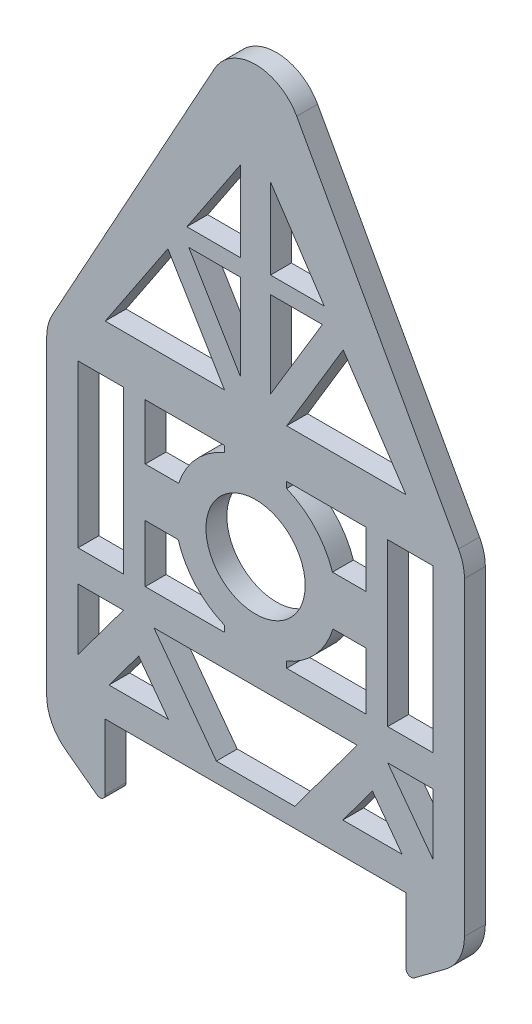
SolidWorks part; units mm, degrees
ref_plane "Front Plane" through (0, 0, 0) normal (0, 0, 1) x (1, 0, 0)
ref_plane "Top Plane" through (0, 0, 0) normal (0, 1, 0) x (1, 0, 0)
ref_plane "Right Plane" through (0, 0, 0) normal (1, 0, 0) x (0, 0, -1)
sketch "Sketch1" plane through (0, 0, 0) normal (0, 0, 1) x (1, 0, 0)
  line L0 (-99.8035, -268.9774) -> (188.0854, -268.9774)
  line L1 (244.1409, -268.9774) -> (244.1409, 31.0226)
  line L2 (-155.8591, 31.0226) -> (-155.8591, -268.9774)
  line L3 (-155.8591, -268.9774) -> (-155.8591, -299.9668)
  line L4 (244.1409, 31.0226) -> (249.6965, 25.467)
  line L5 (-125.8591, -170.0215) -> (-82.3496, -170.0215)
  line L6 (-125.8591, -228.5924) -> (-82.3496, -170.0215)
  line L7 (6.6435, -250.5962) -> (-53.2114, -170.0215)
  line L8 (81.6384, -250.5962) -> (141.4933, -170.0215)
  line L9 (184.4837, -238.9774) -> (127.6411, -238.9774)
  line L10 (-125.8591, -140.0215) -> (-82.3496, -140.0215)
  line L11 (29.8006, 255.4287) -> (-21.6123, 178.3095)
  line L12 (188.0854, 61.0226) -> (128.0632, 151.0559)
  line L13 (-99.8035, 61.0226) -> (14.3687, 61.0226)
  line L14 (214.1409, -228.5924) -> (170.6315, -170.0215)
  line L15 (-125.8591, 14.9785) -> (-82.3496, 14.9785)
  line L16 (-125.8591, 14.9785) -> (-125.8591, -47.5196)
  line L17 (214.1409, -140.0215) -> (214.1409, -90.1864)
  line L18 (-155.8591, -299.9668) -> (-99.8035, -341.6077)
  line L19 (-67.7805, -153.2239) -> (-67.7805, -177.2767) construction
  line L20 (127.6411, -238.9774) -> (156.0624, -200.7176)
  line L21 (6.6435, -250.5962) -> (81.6384, -250.5962)
  line L22 (184.4837, -238.9774) -> (156.0624, -200.7176)
  line L23 (-96.2018, -238.9774) -> (-39.3592, -238.9774)
  line L24 (73.9132, 61.0226) -> (188.0854, 61.0226)
  line L25 (-96.2018, -238.9774) -> (-67.7805, -200.7176)
  line L26 (170.6315, -170.0215) -> (214.1409, -170.0215)
  line L27 (-53.2114, -170.0215) -> (141.4933, -170.0215)
  line L28 (-39.3592, -238.9774) -> (-67.7805, -200.7176)
  line L29 (-99.8035, -341.6077) -> (-99.8035, -268.9774)
  line L30 (188.0854, -341.6077) -> (188.0854, -268.9774)
  line L31 (-21.6123, 178.3095) -> (29.8006, 178.3095)
  line L32 (44.1409, 155.8781) -> (44.1409, 393.9988) construction
  line L33 (-155.8591, 31.0226) -> (44.1409, 393.9988)
  line L34 (44.1409, 155.8781) -> (44.1409, 84.5085) construction
  line L35 (44.1409, 393.9988) -> (244.1409, 31.0226)
  line L36 (-82.3496, 14.9785) -> (-82.3496, -47.5196)
  line L37 (-61.486, 14.9785) -> (-61.486, -38.3668)
  line L38 (-323.7476, -62.5215) -> (-253.6301, -62.5215) construction
  line L39 (-82.3496, -140.0215) -> (-82.3496, -90.1864)
  line L40 (-61.486, -140.0215) -> (-61.486, -85.2553)
  line L41 (244.1409, -299.9668) -> (188.0854, -341.6077)
  line L42 (244.1409, -268.9774) -> (244.1409, -299.9668)
  line L43 (-155.8591, -268.9774) -> (-155.8591, -299.9668)
  line L44 (244.1409, -268.9774) -> (244.1409, -299.9668)
  line L45 (-125.8591, -170.0215) -> (-125.8591, -228.5924)
  line L46 (214.1409, -170.0215) -> (214.1409, -228.5924)
  line L47 (14.3687, -134.0747) -> (14.3687, -140.0215)
  line L48 (73.9132, -134.0747) -> (73.9132, -140.0215)
  line L49 (14.3687, 9.0317) -> (14.3687, 14.9785)
  line L50 (73.9132, 9.0317) -> (73.9132, 14.9785)
  line L51 (149.7679, -140.0215) -> (149.7679, -85.2553)
  line L52 (170.6315, -140.0215) -> (170.6315, -90.1864)
  line L53 (149.7679, 14.9785) -> (149.7679, -38.3668)
  line L54 (170.6315, 14.9785) -> (170.6315, -47.5196)
  line L55 (-125.8591, -90.1864) -> (-125.8591, -140.0215)
  line L56 (108.1248, 162.1051) -> (58.4813, 162.1051)
  line L57 (109.8942, 178.3095) -> (58.4813, 255.4287)
  line L58 (29.8006, 255.4287) -> (29.8006, 178.3095)
  line L59 (58.4813, 255.4287) -> (58.4813, 178.3095)
  line L60 (-19.8429, 162.1051) -> (29.8006, 79.5646)
  line L61 (-39.7813, 151.0559) -> (14.3687, 61.0226)
  line L62 (108.1248, 162.1051) -> (58.4813, 79.5646)
  line L63 (128.0632, 151.0559) -> (73.9132, 61.0226)
  line L64 (58.4813, 178.3095) -> (109.8942, 178.3095)
  line L65 (29.8006, 162.1051) -> (-19.8429, 162.1051)
  line L66 (29.8006, 162.1051) -> (29.8006, 79.5646)
  line L67 (58.4813, 162.1051) -> (58.4813, 79.5646)
  line L68 (-39.7813, 151.0559) -> (-99.8035, 61.0226)
  line L69 (214.1409, -47.5196) -> (214.1409, 14.9785)
  line L70 (149.7679, -85.2553) -> (118.2316, -85.2553)
  line L71 (149.7679, -38.3668) -> (117.7806, -38.3668)
  line L72 (-61.486, -85.2553) -> (-29.9497, -85.2553)
  line L73 (-61.486, -38.3668) -> (-29.4987, -38.3668)
  line L74 (-61.486, 14.9785) -> (14.3687, 14.9785)
  line L75 (-61.486, -140.0215) -> (14.3687, -140.0215)
  line L76 (170.6315, -140.0215) -> (214.1409, -140.0215)
  line L77 (170.6315, 14.9785) -> (214.1409, 14.9785)
  line L78 (73.9132, 14.9785) -> (149.7679, 14.9785)
  line L79 (73.9132, -140.0215) -> (149.7679, -140.0215)
  line L80 (214.1409, -47.5196) -> (214.1409, -90.1864)
  line L81 (170.6315, -47.5196) -> (170.6315, -90.1864)
  line L82 (-82.3496, -47.5196) -> (-82.3496, -90.1864)
  line L83 (-125.8591, -47.5196) -> (-125.8591, -90.1864)
  arc A0 (-29.9497, -85.2553) -> (14.3687, -134.0747) centre (44.1409, -62.5215) ccw
  circle A1 centre (44.1409, -62.5215) radius 47.5
  arc A2 (117.7806, -38.3668) -> (73.9132, 9.0317) centre (44.1409, -62.5215) ccw
  arc A3 (14.3687, 9.0317) -> (-29.4987, -38.3668) centre (44.1409, -62.5215) ccw
  arc A4 (73.9132, -134.0747) -> (118.2316, -85.2553) centre (44.1409, -62.5215) ccw
  point P42 (-82.3496, -115.1039)
  point P55 (170.6315, -115.1039)
  point P92 (-104.1043, -140.0215)
  dimension "D1" = 400
  dimension "D2" = 53.393
  dimension "D3" = 155
extrude "Boss-Extrude1" add sketch "Sketch1" along normal blind 20 contours L42 L1 L35 L33 L2 L3 L18 L29 L0 L30 L41 A1 L83 L16 L15 L36 L82 L39 L10 L55 L81 L54 L77 L69 L80 L17 L76 L52 L68 L61 L13 L67 L56 L62 L64 L59 L57 L63 L12 L24 L45 L5 L6
fillet "Fillet1" radius 45 5 edges at (244.1409, -299.9668, 10) (-155.8591, -299.9668, 10) (244.1409, 31.0226, 10) (-155.8591, 31.0226, 10) (44.1409, 393.9988, 10)
fillet "Fillet2" radius 5 2 edges at (188.0854, -341.6077, 10) (-99.8035, -341.6077, 10)
